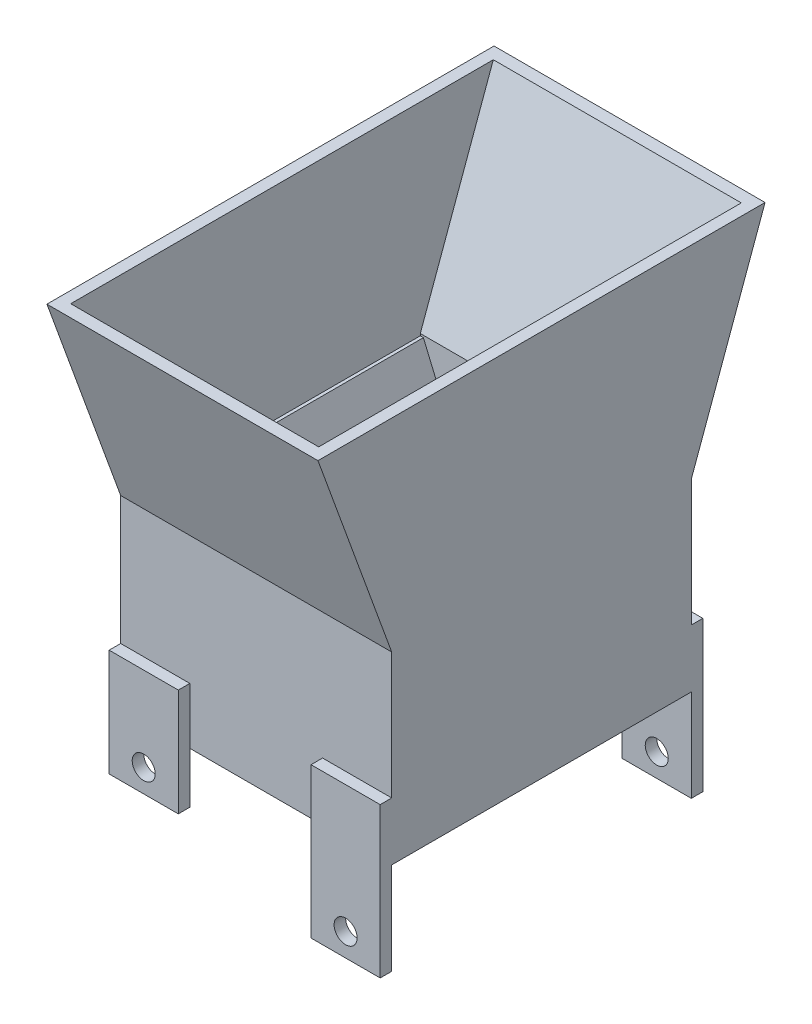
SolidWorks part; units mm, degrees
ref_plane "Front Plane" through (0, 0, 0) normal (0, 0, 1) x (1, 0, 0)
ref_plane "Top Plane" through (0, 0, 0) normal (0, 1, 0) x (1, 0, 0)
ref_plane "Right Plane" through (0, 0, 0) normal (1, 0, 0) x (0, 0, -1)
sketch "Sketch4" plane through (0, 0, 0) normal (1, 0, 0) x (0, 0, -1)
  line L6 (-44.9156, 37.0436) -> (78.2744, 37.0436)
  line L7 (78.2744, 37.0436) -> (57.9544, -18.7852)
  line L8 (57.9544, -18.7852) -> (57.9544, -69.5852)
  line L9 (57.9544, -69.5852) -> (-24.5956, -69.5852)
  line L10 (-24.5956, -69.5852) -> (-24.5956, -18.7852)
  line L11 (-24.5956, -18.7852) -> (-44.9156, 37.0436)
  point P12 (-15.0706, -84.3982)
  dimension "D1" = 82.55
  dimension "D2" = 50.8
  dimension "D3" = 160
  dimension "D4" = 160
  dimension "D5" = 20.32
extrude "Boss-Extrude2" add sketch "Sketch4" along normal blind 74.676
shell "Shell1" thickness 3.175
sketch "Sketch6" plane through (0, 0, 21.4206) normal (0, 0, -1) x (-1, 0, 0)
  line L0 (-4.03, -18.7852) -> (-25.4, -69.5852)
  line L1 (-74.676, -69.5852) -> (0, -69.5852) construction
  line L2 (-74.676, -18.7852) -> (0, -18.7852) construction
  line L7 (0, -18.7852) -> (-22.225, -69.5852)
  line L8 (-22.225, -69.5852) -> (-25.4, -69.5852)
  line L9 (-4.03, -18.7852) -> (0, -18.7852)
  point P3 (0, 0)
  point P7 (0, 0)
  point P9 (0, 0)
  dimension "D1" = 3.175
extrude "Boss-Extrude3" add sketch "Sketch6" along normal up to next
sketch "Sketch7" plane through (0, 0, -57.9544) normal (0, 0, -1) x (-1, 0, 0)
  line L0 (-74.676, -53.612) -> (-55.626, -53.612)
  line L1 (-74.676, -69.5852) -> (-74.676, -18.7852) construction
  line L2 (-55.626, -53.612) -> (-55.626, -94.9852)
  line L3 (-55.626, -94.9852) -> (-74.676, -94.9852)
  line L4 (-74.676, -94.9852) -> (-74.676, -53.612)
  line L5 (0, -69.5852) -> (0, -18.7852) construction
  line L6 (0, -54.0924) -> (-19.05, -54.0924)
  line L7 (0, -54.0924) -> (0, -83.6421)
  line L8 (0, -83.6421) -> (-19.05, -83.6421)
  line L9 (-19.05, -54.0924) -> (-19.05, -83.6421)
  line L10 (-74.676, -69.5852) -> (0, -69.5852) construction
  circle A0 centre (-65.151, -88.6352) radius 3.175
  circle A1 centre (-9.525, -77.2921) radius 3.175
  point P12 (-65.151, -88.6352)
  point P13 (-9.525, -77.2921)
  dimension "D7" = 19.05
  dimension "D1" = 19.05
  dimension "D2" = 19.05
  dimension "D3" = 9.525
  dimension "D4" = 9.525
  dimension "D5" = 6.35
  dimension "D6" = 6.35
extrude "Boss-Extrude4" add sketch "Sketch7" along normal blind 3.175
ref_plane "Plane1" through (0, 0, -16.6794) normal (0, 0, -1) x (-1, 0, 0)
mirror "Mirror1" about plane through (0, 0, -16.6794) normal (0, 0, -1) of "Boss-Extrude4"
